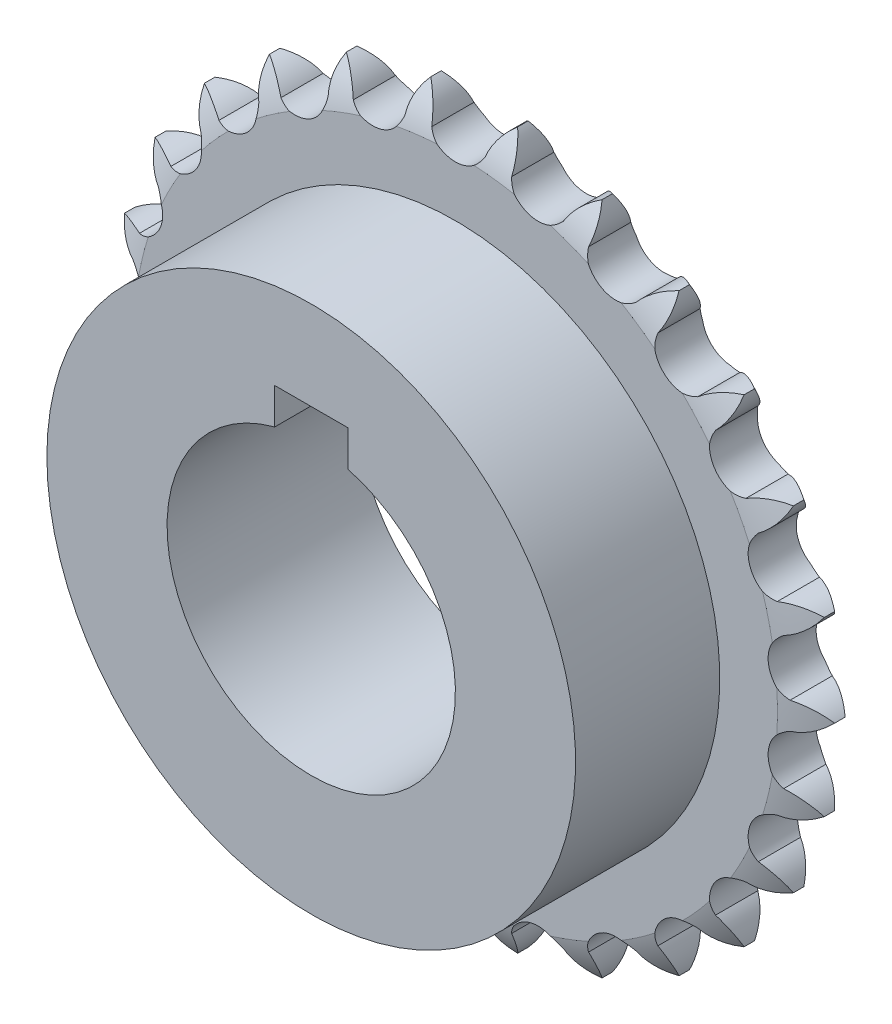
SolidWorks part; units mm, degrees
ref_plane "Front Plane" through (0, 0, 0) normal (0, 0, 1) x (1, 0, 0)
ref_plane "Top Plane" through (0, 0, 0) normal (0, 1, 0) x (1, 0, 0)
ref_plane "Right Plane" through (0, 0, 0) normal (1, 0, 0) x (0, 0, -1)
sketch "Sketch2" plane through (0, 0, 0) normal (1, 0, 0) x (0, 0, -1)
  line L0 (0, 0) -> (-25.4, 0) construction
  line L1 (-25.4, 19.05) -> (0, 19.05)
  line L2 (0, 19.05) -> (0, 42.545)
  line L3 (-25.4, 19.05) -> (-25.4, 34.925)
  line L4 (-25.4, 34.925) -> (-6.35, 34.925)
  line L5 (-3.8608, 47.625) -> (-2.4892, 47.625)
  line L6 (-6.35, 34.925) -> (0, 34.925) construction
  line L7 (-3.175, 47.625) -> (-3.175, 34.925) construction
  line L8 (-6.35, 34.925) -> (-6.35, 42.545)
  arc A3 (0, 42.545) -> (-2.4892, 47.625) centre (-12.3626, 39.6372) ccw
  arc A4 (-6.35, 42.545) -> (-3.8608, 47.625) centre (6.0126, 39.6372) cw
  point P13 (0, 56.6954)
  point P16 (-1.2192, 60.3755)
  point P17 (0, 55.7002)
  point P18 (-1.2192, 60.9078)
  point P20 (0, 42.6988)
  dimension "D6" = 12.7
  dimension "D1" = 25.4
  dimension "D2" = 19.05
  dimension "D3" = 34.925
  dimension "D4" = 19.05
  dimension "D5" = 1.3716
  dimension "D7" = 12.7
  dimension "D8" = 5.08
revolve "Revolve1" add sketch "Sketch2" angle 360 about L0
sketch "Sketch3" plane through (0, 0, 25.4) normal (0, 0, 1) x (1, 0, 0)
  line L0 (0, 0) -> (0, 47.625) construction
  line L1 (0, 0) -> (11.3974, 46.2411) construction
  line L2 (0, 0) -> (5.7421, 47.2776) construction
  line L3 (7.0494, 43.2945) -> (5.2844, 43.5089) construction
  line L4 (5.2844, 43.5089) -> (3.5194, 43.7233) construction
  line L5 (17.2057, 40.3494) -> (15.5432, 40.98) construction
  line L6 (15.5432, 40.98) -> (13.8808, 41.6105) construction
  line L7 (0, 0) -> (16.8896, 44.5296) construction
  line L8 (26.3619, 35.0594) -> (24.8987, 36.0694) construction
  line L9 (24.8987, 36.0694) -> (23.4355, 37.0795) construction
  line L10 (0, 0) -> (27.0554, 39.1937) construction
  line L11 (33.9862, 27.7318) -> (32.8072, 29.0627) construction
  line L12 (32.8072, 29.0627) -> (31.6282, 30.3936) construction
  line L13 (0, 0) -> (35.6489, 31.58) construction
  line L14 (39.6352, 18.7925) -> (38.809, 20.3669) construction
  line L15 (38.809, 20.3669) -> (37.9828, 21.9413) construction
  line L16 (0, 0) -> (42.1706, 22.131) construction
  line L17 (42.9809, 8.7611) -> (42.5554, 10.4875) construction
  line L18 (42.5554, 10.4875) -> (42.13, 12.2138) construction
  line L19 (0, 0) -> (46.2415, 11.3959) construction
  line L20 (43.8286, -1.7795) -> (43.8286, -0.0015) construction
  line L21 (43.8286, -0.0015) -> (43.8287, 1.7765) construction
  line L22 (0, 0) -> (47.625, -0.0016) construction
  line L23 (42.1291, -12.2166) -> (42.5547, -10.4903) construction
  line L24 (42.5547, -10.4903) -> (42.9803, -8.764) construction
  line L25 (0, 0) -> (46.2407, -11.399) construction
  line L26 (37.9813, -21.9438) -> (38.8077, -20.3695) construction
  line L27 (38.8077, -20.3695) -> (39.634, -18.7952) construction
  line L28 (0, 0) -> (42.1691, -22.1339) construction
  line L29 (31.6262, -30.3957) -> (32.8052, -29.0649) construction
  line L30 (32.8052, -29.0649) -> (33.9843, -27.7341) construction
  line L31 (0, 0) -> (35.6468, -31.5824) construction
  line L32 (23.433, -37.0811) -> (24.8963, -36.0711) construction
  line L33 (24.8963, -36.0711) -> (26.3596, -35.0611) construction
  line L34 (0, 0) -> (27.0528, -39.1955) construction
  line L35 (13.878, -41.6114) -> (15.5405, -40.981) construction
  line L36 (15.5405, -40.981) -> (17.203, -40.3506) construction
  line L37 (0, 0) -> (16.8866, -44.5307) construction
  line L38 (3.5165, -43.7235) -> (5.2815, -43.5093) construction
  line L39 (5.2815, -43.5093) -> (7.0465, -43.295) construction
  line L40 (0, 0) -> (5.739, -47.278) construction
  line L41 (-7.0494, -43.2945) -> (-5.2844, -43.5089) construction
  line L42 (-5.2844, -43.5089) -> (-3.5194, -43.7233) construction
  line L43 (0, 0) -> (-5.7421, -47.2776) construction
  line L44 (-17.2057, -40.3494) -> (-15.5432, -40.98) construction
  line L45 (-15.5432, -40.98) -> (-13.8808, -41.6105) construction
  line L46 (0, 0) -> (-16.8896, -44.5296) construction
  line L47 (-26.3619, -35.0594) -> (-24.8987, -36.0694) construction
  line L48 (-24.8987, -36.0694) -> (-23.4355, -37.0795) construction
  line L49 (0, 0) -> (-27.0554, -39.1937) construction
  line L50 (-33.9862, -27.7318) -> (-32.8072, -29.0627) construction
  line L51 (-32.8072, -29.0627) -> (-31.6282, -30.3936) construction
  line L52 (0, 0) -> (-35.6489, -31.58) construction
  line L53 (-39.6352, -18.7925) -> (-38.809, -20.3669) construction
  line L54 (-38.809, -20.3669) -> (-37.9828, -21.9413) construction
  line L55 (0, 0) -> (-42.1706, -22.131) construction
  line L56 (-42.9809, -8.7611) -> (-42.5554, -10.4875) construction
  line L57 (-42.5554, -10.4875) -> (-42.13, -12.2138) construction
  line L58 (0, 0) -> (-46.2415, -11.3959) construction
  line L59 (-43.8286, 1.7795) -> (-43.8286, 0.0015) construction
  line L60 (-43.8286, 0.0015) -> (-43.8287, -1.7765) construction
  line L61 (0, 0) -> (-47.625, 0.0016) construction
  line L62 (-42.1291, 12.2166) -> (-42.5547, 10.4903) construction
  line L63 (-42.5547, 10.4903) -> (-42.9803, 8.764) construction
  line L64 (0, 0) -> (-46.2407, 11.399) construction
  line L65 (-37.9813, 21.9438) -> (-38.8077, 20.3695) construction
  line L66 (-38.8077, 20.3695) -> (-39.634, 18.7952) construction
  line L67 (0, 0) -> (-42.1691, 22.1339) construction
  line L68 (-31.6262, 30.3957) -> (-32.8052, 29.0649) construction
  line L69 (-32.8052, 29.0649) -> (-33.9843, 27.7341) construction
  line L70 (0, 0) -> (-35.6468, 31.5824) construction
  line L71 (-23.433, 37.0811) -> (-24.8963, 36.0711) construction
  line L72 (-24.8963, 36.0711) -> (-26.3596, 35.0611) construction
  line L73 (0, 0) -> (-27.0528, 39.1955) construction
  line L74 (-13.878, 41.6114) -> (-15.5405, 40.981) construction
  line L75 (-15.5405, 40.981) -> (-17.203, 40.3506) construction
  line L76 (0, 0) -> (-16.8866, 44.5307) construction
  line L77 (-3.5165, 43.7235) -> (-5.2815, 43.5093) construction
  line L78 (-5.2815, 43.5093) -> (-7.0465, 43.295) construction
  line L79 (0, 0) -> (-5.739, 47.278) construction
  circle A0 centre (0, 0) radius 47.625 construction
  arc A4 (5.7421, 47.2776) -> (7.0494, 43.2945) centre (1.2147, 43.5855) cw
  arc A5 (5.7421, 47.2776) -> (3.5194, 43.7233) centre (9.2542, 42.6091) ccw
  arc A7 (16.8896, 44.5296) -> (17.2057, 40.3494) centre (11.6101, 42.0283) cw
  arc A8 (16.8896, 44.5296) -> (13.8808, 41.6105) centre (19.1823, 39.1563) ccw
  arc A9 (27.0554, 39.1937) -> (26.3619, 35.0594) centre (21.3308, 38.0286) cw
  arc A10 (27.0554, 39.1937) -> (23.4355, 37.0795) centre (27.9956, 33.4278) ccw
  arc A11 (35.6489, 31.58) -> (33.9862, 27.7318) centre (29.8118, 31.8187) cw
  arc A12 (35.6489, 31.58) -> (31.6282, 30.3936) centre (35.1819, 25.7567) ccw
  arc A13 (42.1706, 22.131) -> (39.6352, 18.7925) centre (36.5602, 23.7597) cw
  arc A14 (42.1706, 22.131) -> (37.9828, 21.9413) centre (40.3235, 16.5887) ccw
  arc A15 (46.2415, 11.3959) -> (42.9809, 8.7611) centre (41.1839, 14.3199) cw
  arc A16 (46.2415, 11.3959) -> (42.13, 12.2138) centre (43.1218, 6.4566) ccw
  arc A17 (47.625, -0.0016) -> (43.8286, -1.7795) centre (43.4142, 4.0478) cw
  arc A18 (47.625, -0.0016) -> (43.8287, 1.7765) centre (43.4139, -4.0507) ccw
  arc A19 (46.2407, -11.399) -> (42.1291, -12.2166) centre (43.1213, -6.4595) cw
  arc A20 (46.2407, -11.399) -> (42.9803, -8.764) centre (41.1829, -14.3226) ccw
  arc A21 (42.1691, -22.1339) -> (37.9813, -21.9438) centre (40.3224, -16.5914) cw
  arc A22 (42.1691, -22.1339) -> (39.634, -18.7952) centre (36.5586, -23.7622) ccw
  arc A23 (35.6468, -31.5824) -> (31.6262, -30.3957) centre (35.1802, -25.7591) cw
  arc A24 (35.6468, -31.5824) -> (33.9843, -27.7341) centre (29.8096, -31.8207) ccw
  arc A25 (27.0528, -39.1955) -> (23.433, -37.0811) centre (27.9933, -33.4297) cw
  arc A26 (27.0528, -39.1955) -> (26.3596, -35.0611) centre (21.3282, -38.03) ccw
  arc A27 (16.8866, -44.5307) -> (13.878, -41.6114) centre (19.1796, -39.1576) cw
  arc A28 (16.8866, -44.5307) -> (17.203, -40.3506) centre (11.6073, -42.0291) ccw
  arc A29 (5.739, -47.278) -> (3.5165, -43.7235) centre (9.2513, -42.6097) cw
  arc A30 (5.739, -47.278) -> (7.0465, -43.295) centre (1.2118, -43.5856) ccw
  arc A31 (-5.7421, -47.2776) -> (-7.0494, -43.2945) centre (-1.2147, -43.5855) cw
  arc A32 (-5.7421, -47.2776) -> (-3.5194, -43.7233) centre (-9.2542, -42.6091) ccw
  arc A33 (-16.8896, -44.5296) -> (-17.2057, -40.3494) centre (-11.6101, -42.0283) cw
  arc A34 (-16.8896, -44.5296) -> (-13.8808, -41.6105) centre (-19.1823, -39.1563) ccw
  arc A35 (-27.0554, -39.1937) -> (-26.3619, -35.0594) centre (-21.3308, -38.0286) cw
  arc A36 (-27.0554, -39.1937) -> (-23.4355, -37.0795) centre (-27.9956, -33.4278) ccw
  arc A37 (-35.6489, -31.58) -> (-33.9862, -27.7318) centre (-29.8118, -31.8187) cw
  arc A38 (-35.6489, -31.58) -> (-31.6282, -30.3936) centre (-35.1819, -25.7567) ccw
  arc A39 (-42.1706, -22.131) -> (-39.6352, -18.7925) centre (-36.5602, -23.7597) cw
  arc A40 (-42.1706, -22.131) -> (-37.9828, -21.9413) centre (-40.3235, -16.5887) ccw
  arc A41 (-46.2415, -11.3959) -> (-42.9809, -8.7611) centre (-41.1839, -14.3199) cw
  arc A42 (-46.2415, -11.3959) -> (-42.13, -12.2138) centre (-43.1218, -6.4566) ccw
  arc A43 (-47.625, 0.0016) -> (-43.8286, 1.7795) centre (-43.4142, -4.0478) cw
  arc A44 (-47.625, 0.0016) -> (-43.8287, -1.7765) centre (-43.4139, 4.0507) ccw
  arc A45 (-46.2407, 11.399) -> (-42.1291, 12.2166) centre (-43.1213, 6.4595) cw
  arc A46 (-46.2407, 11.399) -> (-42.9803, 8.764) centre (-41.1829, 14.3226) ccw
  arc A47 (-42.1691, 22.1339) -> (-37.9813, 21.9438) centre (-40.3224, 16.5914) cw
  arc A48 (-42.1691, 22.1339) -> (-39.634, 18.7952) centre (-36.5586, 23.7622) ccw
  arc A49 (-35.6468, 31.5824) -> (-31.6262, 30.3957) centre (-35.1802, 25.7591) cw
  arc A50 (-35.6468, 31.5824) -> (-33.9843, 27.7341) centre (-29.8096, 31.8207) ccw
  arc A51 (-27.0528, 39.1955) -> (-23.433, 37.0811) centre (-27.9933, 33.4297) cw
  arc A52 (-27.0528, 39.1955) -> (-26.3596, 35.0611) centre (-21.3282, 38.03) ccw
  arc A53 (-16.8866, 44.5307) -> (-13.878, 41.6114) centre (-19.1796, 39.1576) cw
  arc A54 (-16.8866, 44.5307) -> (-17.203, 40.3506) centre (-11.6073, 42.0291) ccw
  arc A55 (-5.739, 47.278) -> (-3.5165, 43.7235) centre (-9.2513, 42.6097) cw
  arc A56 (-5.739, 47.278) -> (-7.0465, 43.295) centre (-1.2118, 43.5856) ccw
  arc A57 (-3.5165, 43.7235) -> (3.5194, 43.7233) centre (0.0015, 45.6547) ccw
  circle A58 centre (0, 0) radius 43.8647 construction
  arc A59 (7.0494, 43.2945) -> (13.8808, 41.6105) centre (10.9274, 44.3277) ccw
  arc A60 (17.2057, 40.3494) -> (23.4355, 37.0795) centre (21.2182, 40.4245) ccw
  arc A61 (26.3619, 35.0594) -> (31.6282, 30.3936) centre (30.2758, 34.172) ccw
  arc A62 (33.9862, 27.7318) -> (37.9828, 21.9413) centre (37.574, 25.9336) ccw
  arc A63 (39.6352, 18.7925) -> (42.13, 12.2138) centre (42.6884, 16.188) ccw
  arc A64 (42.9809, 8.7611) -> (43.8287, 1.7765) centre (45.322, 5.5015) ccw
  arc A65 (43.8286, -1.7795) -> (42.9803, -8.764) centre (45.3217, -5.5046) ccw
  arc A66 (42.1291, -12.2166) -> (39.634, -18.7952) centre (42.6874, -16.1908) ccw
  arc A67 (37.9813, -21.9438) -> (33.9843, -27.7341) centre (37.5722, -25.9361) ccw
  arc A68 (31.6262, -30.3957) -> (26.3596, -35.0611) centre (30.2735, -34.1741) ccw
  arc A69 (23.433, -37.0811) -> (17.203, -40.3506) centre (21.2154, -40.426) ccw
  arc A70 (13.878, -41.6114) -> (7.0465, -43.295) centre (10.9244, -44.3284) ccw
  arc A71 (3.5165, -43.7235) -> (-3.5194, -43.7233) centre (-0.0015, -45.6547) ccw
  arc A72 (-7.0494, -43.2945) -> (-13.8808, -41.6105) centre (-10.9274, -44.3277) ccw
  arc A73 (-17.2057, -40.3494) -> (-23.4355, -37.0795) centre (-21.2182, -40.4245) ccw
  arc A74 (-26.3619, -35.0594) -> (-31.6282, -30.3936) centre (-30.2758, -34.172) ccw
  arc A75 (-33.9862, -27.7318) -> (-37.9828, -21.9413) centre (-37.574, -25.9336) ccw
  arc A76 (-39.6352, -18.7925) -> (-42.13, -12.2138) centre (-42.6884, -16.188) ccw
  arc A77 (-42.9809, -8.7611) -> (-43.8287, -1.7765) centre (-45.322, -5.5015) ccw
  arc A78 (-43.8286, 1.7795) -> (-42.9803, 8.764) centre (-45.3217, 5.5046) ccw
  arc A79 (-42.1291, 12.2166) -> (-39.634, 18.7952) centre (-42.6874, 16.1908) ccw
  arc A80 (-37.9813, 21.9438) -> (-33.9843, 27.7341) centre (-37.5722, 25.9361) ccw
  arc A81 (-31.6262, 30.3957) -> (-26.3596, 35.0611) centre (-30.2735, 34.1741) ccw
  arc A82 (-23.433, 37.0811) -> (-17.203, 40.3506) centre (-21.2154, 40.426) ccw
  arc A83 (-13.878, 41.6114) -> (-7.0465, 43.295) centre (-10.9244, 44.3284) ccw
  circle A84 centre (0, 0) radius 47.625
  point P165 (0, 0)
  point P167 (0, 0)
  point P244 (0, 0)
  dimension "D1" = 26
  dimension "D3" = 6.925
  dimension "D4" = 5.842
  dimension "D5" = 4.0132
  dimension "D6" = 87.7294
  dimension "D2" = 13.846
  dimension "D7" = 1.778
  dimension "D8" = 26
extrude "Cut-Extrude2" cut sketch "Sketch3" against normal through all contours A56 A84 A53 A83 | A5 A84 A55 A57 | A8 A84 A4 A59 | A10 A84 A7 A60 | A12 A84 A9 A61 | A54 A84 A51 A82 | A52 A84 A49 A81 | A50 A84 A47 A80 | A48 A84 A45 A79 | A40 A84 A37 A75 | A42 A84 A39 A76 | A44 A84 A41 A77 | A46 A84 A43 A78 | A14 A84 A11 A62 | A16 A84 A13 A63 | A18 A84 A15 A64 | A20 A84 A17 A65 | A22 A84 A19 A66 | A24 A84 A21 A67 | A28 A84 A25 A69 | A26 A84 A23 A68 | A30 A84 A27 A70 | A32 A84 A29 A71 | A34 A84 A31 A72 | A36 A84 A33 A73 | A38 A84 A35 A74
sketch "Sketch4" plane through (0, 0, 25.4) normal (0, 0, 1) x (1, 0, 0)
  line L0 (0, 0) -> (0, 19.05) construction
  line L1 (-4.826, 18.4286) -> (-4.826, 23.1784)
  line L2 (-4.826, 23.1784) -> (4.826, 23.1784)
  line L3 (4.826, 18.4286) -> (4.826, 23.1784)
  circle A0 centre (0, 0) radius 19.05 construction
  circle A1 centre (0, 0) radius 19.05
  point P11 (0, 23.1784)
  circle M5 centre (0, 0) radius 19.05
  dimension "D1" = 9.652
  dimension "D2" = 4.7498
extrude "Cut-Extrude3" cut sketch "Sketch4" against normal through all contours A1 L3 L2 L1 M5
ref_plane "Plane1" through (0, 0, 3.175) normal (0, 0, 1) x (1, 0, 0)
